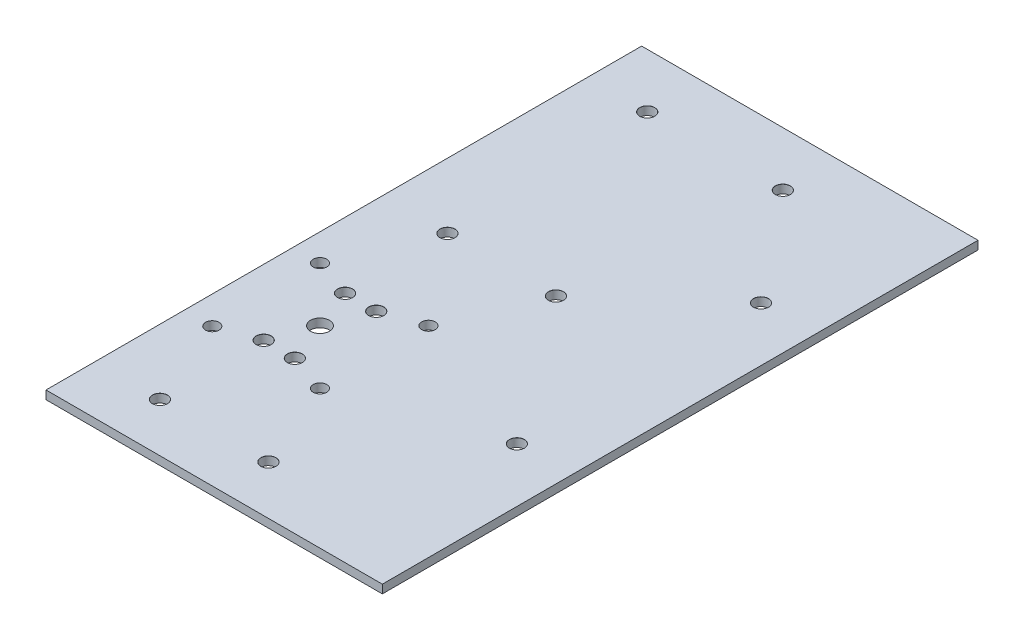
SolidWorks part; units mm, degrees
material "Plain Carbon Steel"
ref_plane "Front Plane" through (0, 0, 0) normal (0, 0, 1) x (1, 0, 0)
ref_plane "Top Plane" through (0, 0, 0) normal (0, 1, 0) x (1, 0, 0)
ref_plane "Right Plane" through (0, 0, 0) normal (1, 0, 0) x (0, 0, -1)
sketch "Sketch1" plane through (0, 0, 0) normal (0, 1, 0) x (1, 0, 0)
  line L1 (0, 0) -> (124, 0)
  line L2 (0, 0) -> (0, 219.6)
  line L3 (0, 219.6) -> (124, 219.6)
  line L4 (124, 0) -> (124, 219.6)
  circle A0 centre (30, 71) radius 3.5
  dimension "D3" = 7
  dimension "D1" = 124
  dimension "D2" = 219.6
  dimension "D4" = 94
  dimension "D5" = 148.6
extrude "Boss-Extrude1" add sketch "Sketch1" along normal blind 3.125
sketch "Sketch2" plane through (0, 3.125, 0) normal (0, 1, 0) x (1, 0, 0)
  line L0 (0, 219.6) -> (0, 0) construction
  line L3 (124, 219.6) -> (0, 219.6) construction
  circle A0 centre (10.3127, 51) radius 2.5
  circle A1 centre (50, 51) radius 2.5
  circle A2 centre (50, 91) radius 2.5
  circle A3 centre (10, 91) radius 2.5
  circle A4 centre (30, 71) radius 3.5 construction
  dimension "D1" = 5
  dimension "D2" = 5
  dimension "D3" = 5
  dimension "D4" = 5
  dimension "D8" = 20
  dimension "D5" = 10
  dimension "D6" = 40
  dimension "D7" = 128.6
extrude "Cut-Extrude1" cut sketch "Sketch2" against normal blind 10
hole_wizard "M5 Clearance Hole1" positions "Sketch8" profile "Sketch6" hole size "M5" standard "ANSI Metric"
sketch "Sketch8" plane through (0, 3.125, 0) normal (0, 1, 0) x (1, 0, 0)
  circle A0 centre (30, 71) radius 3.5 construction
  point P0 (24.25, 86)
  point P2 (35.75, 86)
  point P4 (35.75, 56)
  point P6 (24.25, 56)
  dimension "D1" = 15
  dimension "D5" = 5.75
  dimension "D2" = 5.75
  dimension "D3" = 15
sketch "Sketch6" plane through (24.25, 3.125, -86) normal (1, 0, 0) x (0, 0, 1)
  line L0 (0, 0) -> (0, 11.7524)
  line L1 (0, 11.7524) -> (2.75, 10.1)
  line L2 (2.75, 10.1) -> (2.75, 0.025)
  line L3 (2.75, 0.025) -> (2.775, 0)
  line L5 (2.775, 0) -> (0, 0)
  line L6 (-2.75, 0.025) -> (-2.775, 0) construction
  line L10 (0, 11.7524) -> (-2.75, 10.1) construction
  line L11 (0, -6.35) -> (0, 107.95) construction
  dimension "Hole Dia." = 5.5
  dimension "Hole Depth" = 10.1
  dimension "Near C'Sink Dia." = 5.55
  dimension "Near C'Sink Angle" = 90
  dimension "Drill Angle" = 118
hole_wizard "M5 Clearance Hole2" positions "Sketch11" profile "Sketch10" hole size "M5" standard "ANSI Metric"
sketch "Sketch11" plane through (0, 3.125, 0) normal (0, 1, 0) x (1, 0, 0)
  line L0 (124, 219.6) -> (0, 219.6) construction
  line L1 (124, 0) -> (124, 219.6) construction
  point P0 (22.0496, 199.6)
  point P2 (72.0496, 199.6)
  point P4 (104, 159.6)
  point P6 (104, 69.6)
  dimension "D1" = 20
  dimension "D2" = 20
  dimension "D3" = 50
  dimension "D4" = 90
  dimension "D5" = 60
sketch "Sketch10" plane through (22.0496, 3.125, -199.6) normal (1, 0, 0) x (0, 0, 1)
  line L0 (0, 0) -> (0, 11.7524)
  line L1 (0, 11.7524) -> (2.75, 10.1)
  line L2 (2.75, 10.1) -> (2.75, 0.025)
  line L3 (2.75, 0.025) -> (2.775, 0)
  line L5 (2.775, 0) -> (0, 0)
  line L6 (-2.75, 0.025) -> (-2.775, 0) construction
  line L10 (0, 11.7524) -> (-2.75, 10.1) construction
  line L11 (0, -6.35) -> (0, 107.95) construction
  dimension "Hole Dia." = 5.5
  dimension "Hole Depth" = 10.1
  dimension "Near C'Sink Dia." = 5.55
  dimension "Near C'Sink Angle" = 90
  dimension "Drill Angle" = 118
hole_wizard "M5 Clearance Hole3" positions "Sketch16" profile "Sketch13" hole size "M5" standard "ANSI Metric" end condition through all
sketch "Sketch16" plane through (0, 3.125, 0) normal (0, 1, 0) x (1, 0, 0)
  line L0 (0, 219.6) -> (0, 0) construction
  line L1 (0, 0) -> (124, 0) construction
  point P0 (24, 124)
  point P2 (64, 124)
  point P4 (24, 18)
  point P6 (64, 18)
  dimension "D1" = 24
  dimension "D2" = 64
  dimension "D3" = 106
  dimension "D4" = 18
sketch "Sketch13" plane through (24, 3.125, -124) normal (1, 0, 0) x (0, 0, 1)
  line L0 (0, 0) -> (0, 3.125)
  line L1 (0, 3.125) -> (2.75, 3.125)
  line L2 (2.75, 3.125) -> (2.75, 0.025)
  line L3 (2.75, 0.025) -> (2.775, 0)
  line L5 (2.775, 0) -> (0, 0)
  line L6 (-2.75, 0.025) -> (-2.775, 0) construction
  line L11 (0, -6.35) -> (0, 107.95) construction
  dimension "Thru Hole Dia." = 5.5
  dimension "Thru Hole Depth" = 3.125
  dimension "Near C'Sink Dia." = 5.55
  dimension "Near C'Sink Angle" = 90
